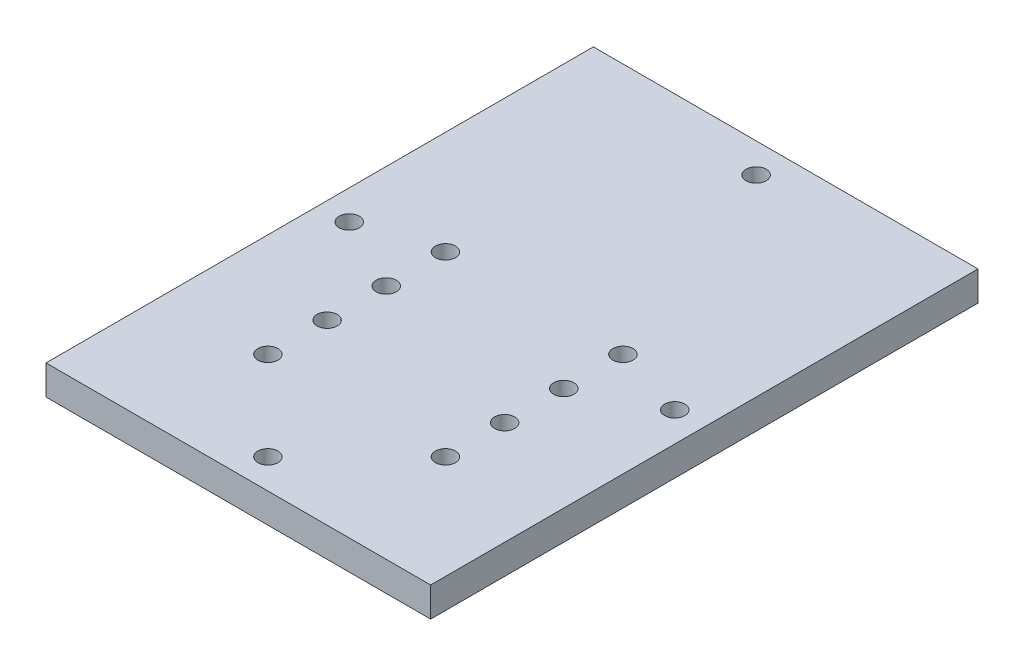
SolidWorks part; units mm, degrees
ref_plane "Front Plane" through (0, 0, 0) normal (0, 0, 1) x (1, 0, 0)
ref_plane "Top Plane" through (0, 0, 0) normal (0, 1, 0) x (1, 0, 0)
ref_plane "Right Plane" through (0, 0, 0) normal (1, 0, 0) x (0, 0, -1)
sketch "Sketch1" plane through (0, 0, 0) normal (0, 1, 0) x (1, 0, 0)
  line L1 (0, 0) -> (-330.2, 0)
  line L2 (0, 0) -> (0, 469.9)
  line L3 (0, 469.9) -> (-330.2, 469.9)
  line L4 (-330.2, 0) -> (-330.2, 469.9)
  circle A0 centre (-165.1, 444.5) radius 8.6487
  circle A2 centre (-25.4, 234.95) radius 8.6487
  circle A3 centre (-165.1, 25.4) radius 8.6487
  circle A4 centre (-304.8, 234.95) radius 8.6487
  circle A5 centre (-88.9, 101.6) radius 8.6487
  circle A6 centre (-88.9, 152.4) radius 8.6487
  circle A7 centre (-88.9, 203.2) radius 8.6487
  circle A8 centre (-88.9, 254) radius 8.6487
  circle A9 centre (-241.3, 101.6) radius 8.6487
  circle A10 centre (-241.3, 152.4) radius 8.6487
  circle A11 centre (-241.3, 203.2) radius 8.6487
  circle A12 centre (-241.3, 254) radius 8.6487
  dimension "D5" = 25.4
  dimension "D11" = 17.2974
  dimension "D12" = 17.2974
  dimension "D13" = 17.2974
  dimension "D14" = 17.2974
  dimension "D15" = 17.2974
  dimension "D16" = 17.2974
  dimension "D17" = 17.2974
  dimension "D18" = 17.2974
  dimension "D19" = 17.2974
  dimension "D20" = 17.2974
  dimension "D21" = 17.2974
  dimension "D22" = 17.2974
  dimension "D1" = 330.2
  dimension "D2" = 469.9
  dimension "D3" = 25.4
  dimension "D4" = 165.1
  dimension "D6" = 234.95
  dimension "D7" = 25.4
  dimension "D8" = 165.1
  dimension "D9" = 25.4
  dimension "D10" = 234.95
  dimension "D23" = 50.8
  dimension "D24" = 50.8
  dimension "D25" = 50.8
  dimension "D26" = 152.4
  dimension "D27" = 50.8
  dimension "D28" = 50.8
  dimension "D29" = 50.8
  dimension "D31" = 88.9
  dimension "D32" = 88.9
  dimension "D33" = 215.9
extrude "Boss-Extrude1" add sketch "Sketch1" along normal blind 25.4
